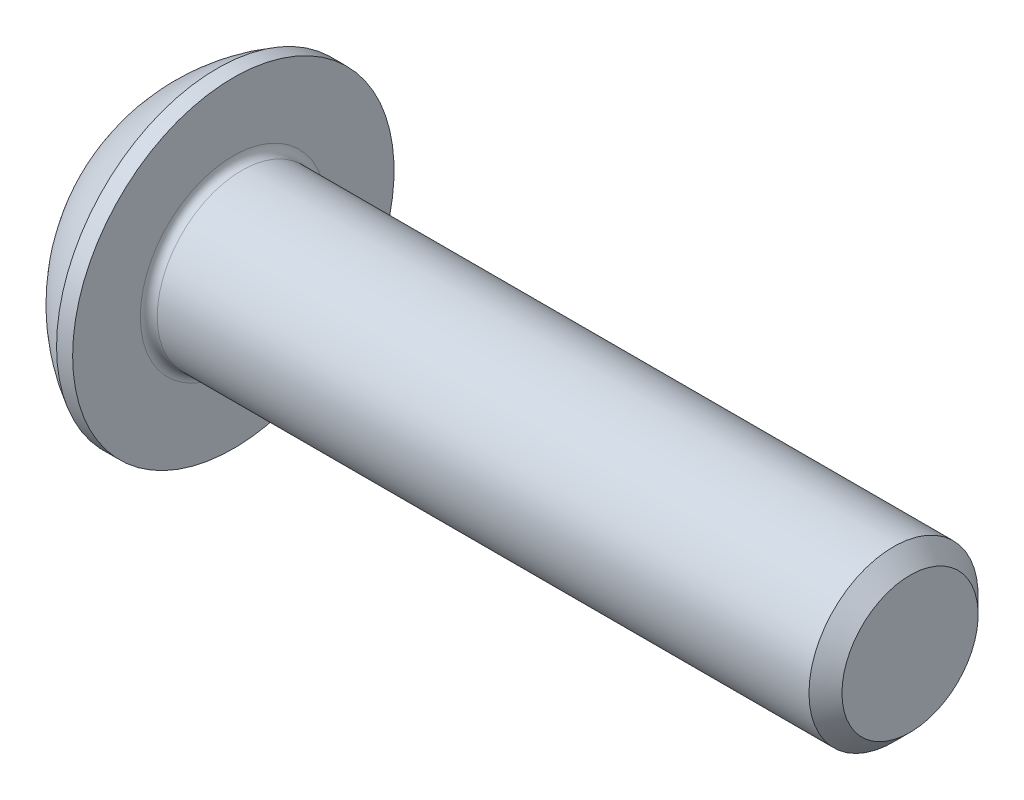
SolidWorks part; units mm, degrees
ref_plane "Plane1" through (0, 0, 0) normal (0, 0, 1) x (1, 0, 0)
ref_plane "Plane2" through (0, 0, 0) normal (0, 1, 0) x (1, 0, 0)
ref_plane "Plane3" through (0, 0, 0) normal (1, 0, 0) x (0, 0, -1)
sketch "BodySke" plane through (0, 0, 0) normal (0, 0, 1) x (1, 0, 0)
  line L0 (18.2, 0) -> (18.2, 1.61)
  line L1 (17.81, 2) -> (2.2, 2)
  line L2 (2.2, 2) -> (2.2, 3.8)
  line L3 (2.2, 3.8) -> (1.82, 3.8)
  line L4 (0, 0) -> (101.6, 0) construction
  line L5 (2.2, -3.8) -> (1.82, -3.8) construction
  line L6 (55.6768, -2) -> (2.2, -2) construction
  line L7 (18.2, 0) -> (0, 0)
  line L8 (0, 1.9) -> (0, -1.9) construction
  line L9 (0, 0) -> (0, 1.9)
  line L10 (18.2, 1.61) -> (17.81, 2)
  line L11 (18.2, -1.61) -> (17.81, -2) construction
  line L12 (2.9, 9.525) -> (2.9, -2) construction
  line L13 (6.2, 9.525) -> (6.2, -2) construction
  arc A1 (0, 1.9) -> (1.82, 3.8) centre (3.8853, 0) cw
  dimension "Diameter" = 4
  dimension "Length" = 16
  dimension "Head_dia" = 7.6
  dimension "D1" = 3.8
  dimension "Head_ht" = 2.2
  dimension "Head_side_ht" = 0.38
  dimension "Minor_dia" = 3.22
  dimension "Body_ch_ang" = 45
  dimension "Advance" = 0.7
revolve "BaseBody" add sketch "BodySke" angle 360 about L4
cosmetic thread "ThreadCosmetic" [suppressed] parameters "Thread_length"=12, "Thread_minor"=3.22
fillet "Fillet1" radius 0.2 1 edges at (2.2, 0, 2)
sketch "Sketch2" plane through (0, 0, 0) normal (0, 0, 1) x (1, 0, 0)
  line L0 (0, 1.25) -> (1.3, 1.25)
  line L1 (1.3, 1.25) -> (2.0217, 0)
  line L3 (2.0217, 0) -> (0, 0)
  line L4 (0, 0) -> (0, 1.25)
  line L5 (0, -1.25) -> (1.3, -1.25) construction
  line L6 (0, 0) -> (47.625, 0) construction
  dimension "D2" = 60
  dimension "PreBroach_depth" = 1.3
  dimension "PreBroach_dia" = 2.5
revolve "PreBroach" cut sketch "Sketch2" angle 360 about L6
sketch "Sketch3" plane through (0, 0, 0) normal (1, 0, 0) x (0, 0, -1)
  line L0 (-1.25, -0.7217) -> (-1.25, 0.7217)
  line L1 (-1.25, 0.7217) -> (0, 1.4434)
  line L2 (0, 1.4434) -> (1.25, 0.7217)
  line L3 (1.25, 0.7217) -> (1.25, -0.7217)
  line L4 (1.25, -0.7217) -> (0, -1.4434)
  line L5 (0, -1.4434) -> (-1.25, -0.7217)
  dimension "Hex_size" = 2.5
  dimension "D3" = 2.5
  dimension "D1" = 1.25
  dimension "D2" = 1.25
extrude "Hex" cut sketch "Sketch3" along normal blind 1.3
sketch "ThdSchSke" plane through (0, 0, 0) normal (0, 0, 1) x (1, 0, 0)
  line L0 (6.2, -1.61) -> (5.9269, -2)
  line L1 (6.2, -1.61) -> (6.4731, -2)
  line L2 (6.4731, -2) -> (6.4731, -2.5)
  line L3 (-3.175, 0) -> (5.1513, 0) construction
  line L5 (6.4731, -2.5) -> (5.9269, -2.5)
  line L6 (5.9269, -2.5) -> (5.9269, -2)
  dimension "Diameter" = 4
  dimension "Thread_minor" = 3.22
  dimension "SideAngle" = 55
  dimension "VeeAngle" = 70
  dimension "Overcut" = 5
revolve "ThreadSchematic" [suppressed] cut sketch "ThdSchSke" angle 360 about L3
pattern_linear "ThdSchPat" [suppressed]
equation "\"D1@BodySke\" = \"Head_dia@BodySke\" * .5"
equation "\"Thread_minor@ThreadCosmetic\" = \"Minor_dia@BodySke\""
equation "\"D1@Sketch3\" = \"Hex_size@Sketch3\" / 2"
equation "\"D2@Sketch3\" = \"D1@Sketch3\""
equation "\"D3@Sketch3\" = \"Hex_size@Sketch3\""
equation "\"Thread_length@ThreadCosmetic\" = ((sgn( (\"Length@BodySke\" - \"Advance@BodySke\" * 2.0) - \"Thread_nom@BodySke\" )-1)*( (\"Length@BodySke\" - \"Advance@BodySke\" * 2.0) - \"Thread_nom@BodySke\" ))/-2+ \"Thread_nom@BodySke\""
equation "\"Thread_minor@ThdSchSke\" = \"Minor_dia@BodySke\""
equation "\"Diameter@ThdSchSke\" = \"Diameter@BodySke\""
equation "\"Overcut@ThdSchSke\" = \"Diameter@BodySke\" * 1.25"
equation "\"Start@ThdSchSke\" = \"Head_ht@BodySke\" + \"Length@BodySke\" - \"Thread_length@ThreadCosmetic\"  '---Non-countersunk---"
equation "\"Num_threads@ThdSchPat\" = int( \"Thread_length@ThreadCosmetic\" / \"Advance@BodySke\" + 0.999 )  + 1"
equation "\"Advance@ThdSchPat\" = \"Thread_length@ThreadCosmetic\" /  (\"Num_threads@ThdSchPat\" - 1) 'relax it"
equation "\"Num_threads@ThdSchPat\" = \"Num_threads@ThdSchPat\" - sgn( \"Num_threads@ThdSchPat\" - 1) '---chamfered tips only---"
